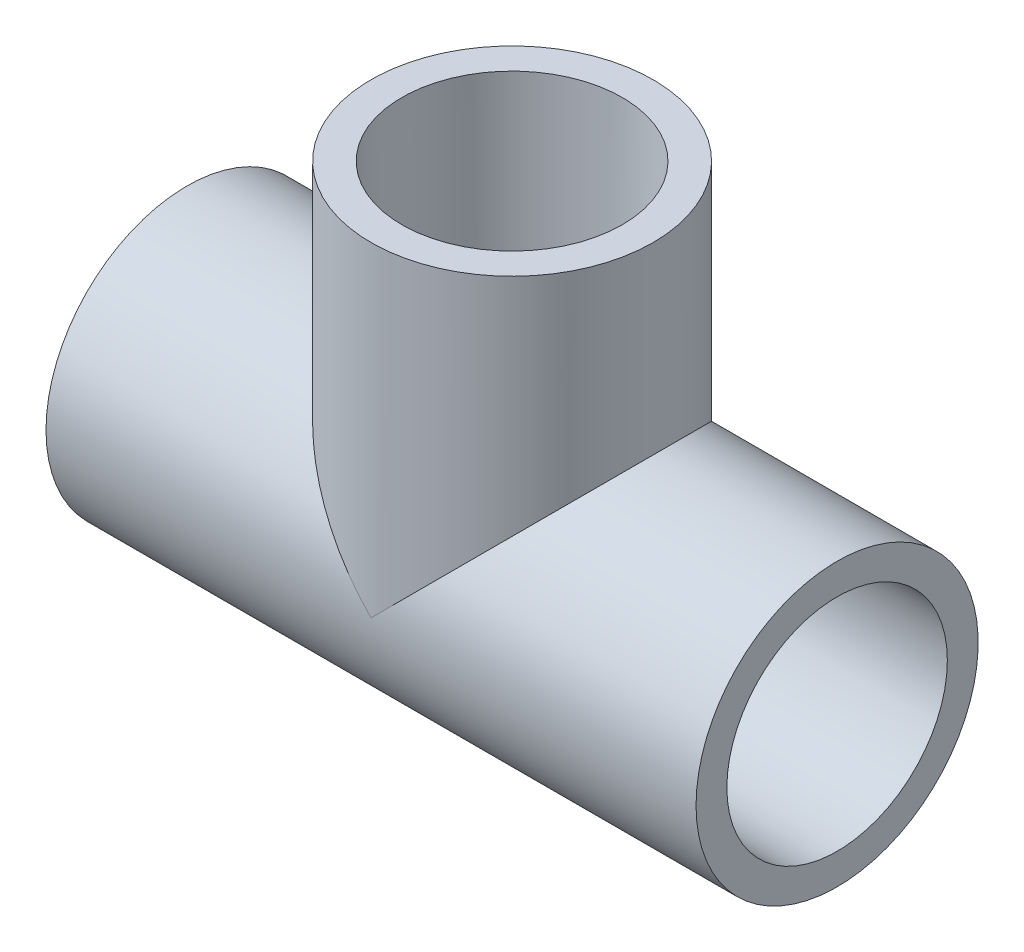
SolidWorks part; units mm, degrees
ref_plane "Front Plane" through (0, 0, 0) normal (0, 0, 1) x (1, 0, 0)
ref_plane "Top Plane" through (0, 0, 0) normal (0, 1, 0) x (1, 0, 0)
ref_plane "Right Plane" through (0, 0, 0) normal (1, 0, 0) x (0, 0, -1)
sketch "Sketch0" plane through (0, 0, 0) normal (0, 0, 1) x (1, 0, 0)
  line L0 (-31.75, 0) -> (0, 0) construction
  line L1 (0, 0) -> (0, 31.75) construction
  line L2 (-12.7, 0) -> (0, 0) construction
  line L3 (0, 0) -> (0, 12.7) construction
  line L4 (-31.75, 13.7795) -> (-31.75, -13.7795) construction
  line L5 (-12.7, 10.6172) -> (-31.75, 10.7696) construction
  line L6 (-12.7, 10.6172) -> (-12.7, -10.6172) construction
  line L7 (-12.7, -10.6172) -> (-31.75, -10.7696) construction
  line L8 (-31.75, 10.7696) -> (-31.75, -10.7696) construction
  line L9 (-13.7795, 31.75) -> (13.7795, 31.75) construction
  line L10 (-10.7696, 31.75) -> (10.7696, 31.75) construction
  line L11 (10.7696, 31.75) -> (10.6172, 12.7) construction
  line L12 (10.6172, 12.7) -> (-10.6172, 12.7) construction
  line L13 (-10.6172, 12.7) -> (-10.7696, 31.75) construction
  line L14 (-12.7, 7.8994) -> (-12.7, -7.8994) construction
  line L15 (-31.75, 0) -> (-12.7, 0) construction
  line L16 (0, 31.75) -> (0, 12.7) construction
  line L17 (0, 0) -> (12.7, 0) construction
  line L18 (-7.8994, 12.7) -> (7.8994, 12.7) construction
  line L19 (12.7, 0) -> (31.75, 0) construction
  dimension "H" = 31.75
  dimension "G" = 12.7
  dimension "M" = 27.559
  dimension "OD A" = 21.5392
  dimension "OD B" = 21.2344
  dimension "ID" = 15.7988
  dimension "H3" = 31.75
sketch "Sketch1" plane through (0, 0, 0) normal (0, 0, 1) x (1, 0, 0)
  line L0 (-31.75, 0) -> (0, 0) construction
  line L1 (-31.75, 0) -> (0, 0) construction
  line L2 (0, 0) -> (0, -13.7795) construction
  line L3 (-31.75, -13.7795) -> (-12.7, -13.7795)
  line L4 (-31.75, -13.7795) -> (-31.75, -10.7696)
  line L5 (-31.75, -10.7696) -> (-12.7, -10.6172)
  line L6 (-12.7, -13.7795) -> (-12.7, -10.6172)
  line L7 (-12.7, -13.7795) -> (0, -13.7795) construction
  line L8 (31.75, -10.7696) -> (12.7, -10.6172)
  line L9 (31.75, -13.7795) -> (31.75, -10.7696)
  line L10 (12.7, -13.7795) -> (12.7, -10.6172)
  line L11 (31.75, -13.7795) -> (12.7, -13.7795)
revolve "Revolve1" add sketch "Sketch1" angle 360 about L1
sketch "Sketch2" plane through (0, 0, 0) normal (0, 0, 1) x (1, 0, 0)
  line L0 (10.7696, 31.75) -> (10.6172, 12.7)
  line L1 (10.6172, 12.7) -> (13.7795, 12.7)
  line L2 (13.7795, 12.7) -> (13.7795, 31.75)
  line L3 (13.7795, 31.75) -> (10.7696, 31.75)
  line L4 (0, 0) -> (0, 31.75) construction
  line L5 (0, 0) -> (0, 31.75) construction
revolve "Revolve2" add sketch "Sketch2" angle 360 about L5
sketch "Sketch3" plane through (-12.7, 0, 0) normal (1, 0, 0) x (0, 0, -1)
  circle A0 centre (0, 0) radius 7.8994
  circle A1 centre (0, 0) radius 13.7795
sketch "Sketch4" plane through (-12.7, 0, 0) normal (1, 0, 0) x (0, 0, -1)
  circle A0 centre (0, 0) radius 13.7795 construction
  circle A1 centre (0, 0) radius 13.7795
extrude "Boss-Extrude1" add sketch "Sketch4" along normal up to vertex
sketch "Sketch5" plane through (0, 12.7, 0) normal (0, -1, 0) x (1, 0, 0)
  circle A0 centre (0, 0) radius 13.7795 construction
  circle A1 centre (0, 0) radius 13.7795
extrude "Boss-Extrude2" add sketch "Sketch5" along normal up to vertex (12.7 mm away) up to point (0, 0, 0)
sketch "Sketch6" plane through (0, 0, 0) normal (0, 0, 1) x (1, 0, 0)
  line L0 (-31.75, -10.7696) -> (-12.7, -10.6172)
  line L1 (-12.7, -10.6172) -> (-12.7, -7.8994)
  line L2 (-12.7, -7.8994) -> (12.7, -7.8994)
  line L3 (12.7, -10.6172) -> (12.7, 9.1728) construction
  line L4 (0, -7.8994) -> (0, 0) construction
  line L5 (12.7, -10.6172) -> (12.7, -7.8994)
  line L6 (31.75, -10.7696) -> (31.75, 10.7696) construction
  line L7 (31.75, -13.7795) -> (31.75, 13.7795) construction
  line L8 (31.75, -10.7696) -> (31.75, 0)
  line L9 (31.75, 0) -> (-31.75, 0)
  line L10 (-31.75, 0) -> (-31.75, -10.7696)
  line L11 (31.75, -10.7696) -> (12.7, -10.6172)
revolve "Cut-Revolve1" cut sketch "Sketch6" angle 360 about L9
sketch "Sketch7" plane through (0, 0, 0) normal (0, 0, 1) x (1, 0, 0)
  line L0 (10.7696, 31.75) -> (10.6172, 12.7)
  line L1 (10.6172, 12.7) -> (7.8994, 12.7)
  line L2 (7.8994, 12.7) -> (7.8994, 0)
  line L3 (0, 0) -> (12.7, 0) construction
  line L4 (7.8994, 0) -> (0, 0)
  line L5 (0, 0) -> (0, 31.75)
  line L6 (-13.7795, 31.75) -> (13.7795, 31.75) construction
  line L7 (0, 31.75) -> (10.7696, 31.75)
revolve "Cut-Revolve2" cut sketch "Sketch7" angle 360 about L5
